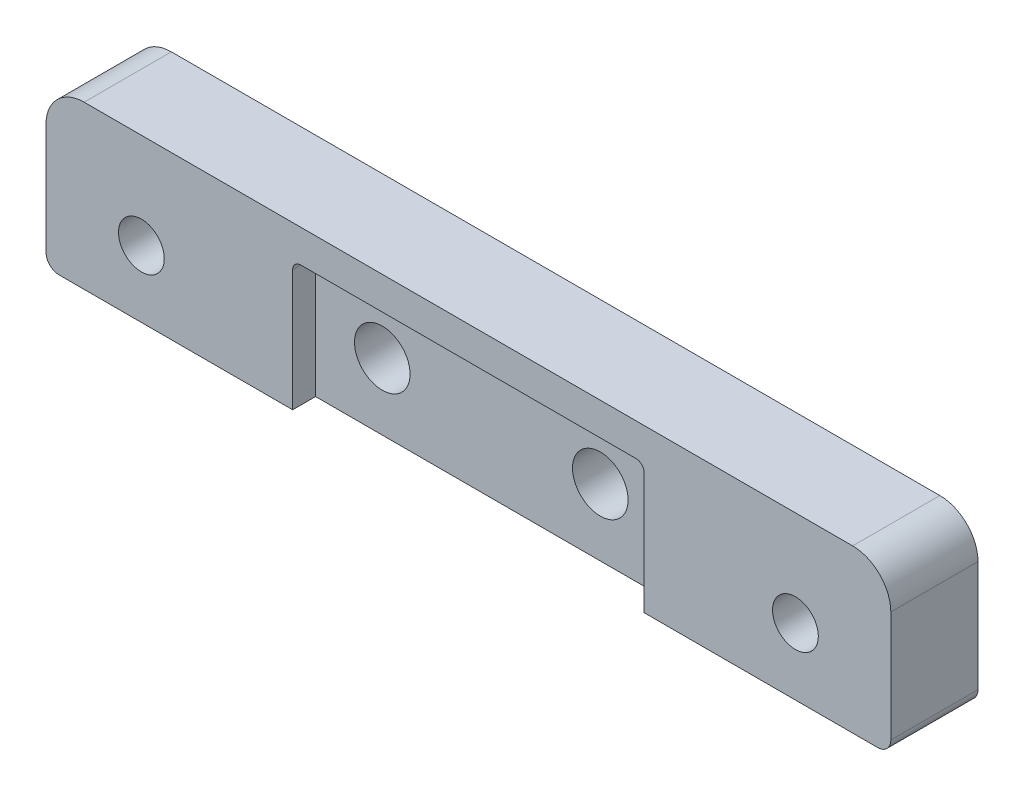
SolidWorks part; units mm, degrees
material "6061-T6 (SS)"
ref_plane "Front Plane" through (0, 0, 0) normal (0, 0, 1) x (1, 0, 0)
ref_plane "Top Plane" through (0, 0, 0) normal (0, 1, 0) x (1, 0, 0)
ref_plane "Right Plane" through (0, 0, 0) normal (1, 0, 0) x (0, 0, -1)
sketch "Sketch1" plane through (0, 0, 0) normal (0, 0, 1) x (1, 0, 0)
  line L1 (38.75, -7.437) -> (-38.75, -7.437)
  line L2 (38.75, -7.437) -> (38.75, 7.437)
  line L3 (38.75, 7.437) -> (-38.75, 7.437)
  line L4 (-38.75, -7.437) -> (-38.75, 7.437)
  line L5 (38.75, -7.437) -> (-38.75, 7.437) construction
  line L6 (38.75, 7.437) -> (-38.75, -7.437) construction
  point P0 (0, 0)
  dimension "D1" = 14.874
  dimension "D3" = 77.5
extrude "Boss-Extrude1" add sketch "Sketch1" along normal blind 8
sketch "Sketch2" plane through (0, 0, 8) normal (0, 0, 1) x (1, 0, 0)
  line L0 (-38.75, -7.437) -> (38.75, -7.437) construction
  line L1 (-16.12, -7.437) -> (16.12, -7.437)
  line L2 (-16.12, -7.437) -> (-16.12, 4.44)
  line L3 (-16.12, 4.44) -> (16.12, 4.44)
  line L4 (16.12, -7.437) -> (16.12, 4.44)
  line L5 (0, 4.44) -> (0, 7.437) construction
  line L6 (38.75, 7.437) -> (-38.75, 7.437) construction
  dimension "D1" = 32.24
  dimension "D2" = 11.877
extrude "Cut-Extrude1" cut sketch "Sketch2" against normal blind 2.1
fillet "Fillet1" radius 3.5 2 edges at (38.75, 7.437, 4) (-38.75, 7.437, 4)
fillet "Fillet2" radius 0.75 2 edges at (16.12, 4.44, 6.95) (-16.12, 4.44, 6.95)
sketch "Sketch3" plane through (0, 0, 5.9) normal (0, 0, 1) x (1, 0, 0)
  line L0 (0, -7.437) -> (0, -12.8587) construction
  line L1 (-16.12, -7.437) -> (16.12, -7.437) construction
  line L2 (35.25, 7.437) -> (-35.25, 7.437) construction
  circle A0 centre (-10, -1.323) radius 2.55
  circle A1 centre (10, -1.323) radius 2.55
  dimension "D1" = 5.1
  dimension "D2" = 20
  dimension "D3" = 8.76
extrude "Cut-Extrude2" cut sketch "Sketch3" against normal through all
hole_wizard "M5x0.8 Tapped Hole1" positions "Sketch5" profile "Sketch4" tap size "M5x0.8" standard "ANSI Metric" end condition through all
sketch "Sketch5" plane through (0, 0, 8) normal (0, 0, 1) x (1, 0, 0)
  line L0 (0, 7.437) -> (0, 17.067) construction
  line L1 (35.25, 7.437) -> (-35.25, 7.437) construction
  point P0 (-30, -1.323)
  point P10 (30, -1.323)
  dimension "D1" = 60
  dimension "D2" = 8.76
sketch "Sketch4" plane through (-30, -1.323, 8) normal (1, 0, 0) x (0, -1, 0)
  line L0 (0, 0) -> (0, 8)
  line L1 (0, 8) -> (2.1, 8)
  line L2 (2.1, 8) -> (2.1, 0)
  line L5 (2.1, 0) -> (0, 0)
  line L11 (0, -6.35) -> (0, 107.95) construction
  dimension "Thread Major Dia." = 4.2
  dimension "Thru Tap Drill Depth" = 8
fillet "Fillet3" radius 1.2 2 edges at (-38.75, -7.437, 4) (38.75, -7.437, 4)
